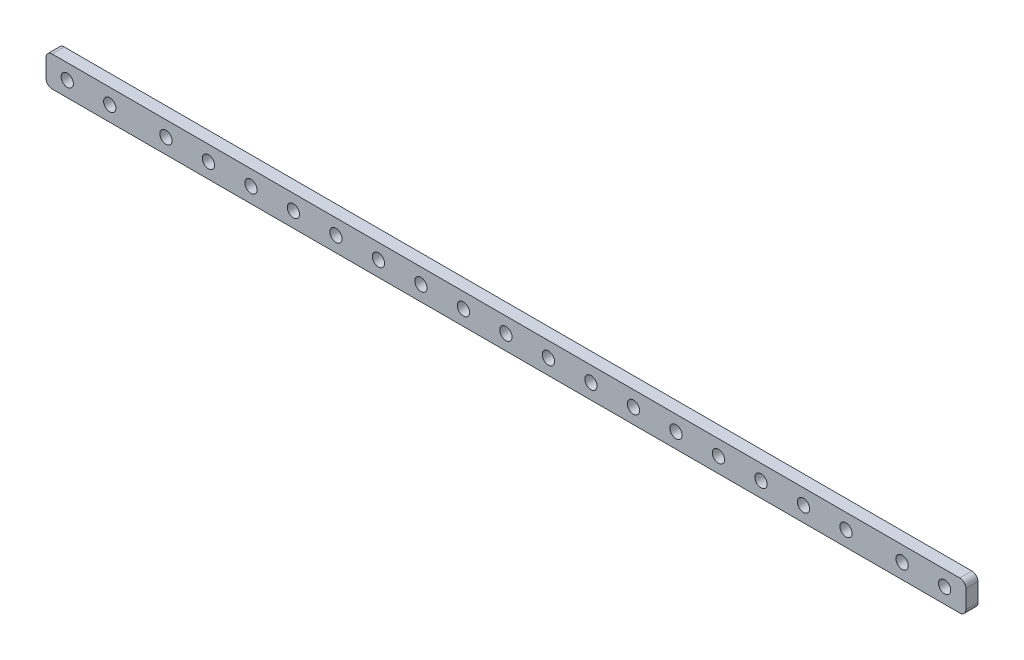
SolidWorks part; units mm, degrees
material "Thornel Mat VMA"
ref_plane "前视基准面" through (0, 0, 0) normal (0, 0, 1) x (1, 0, 0)
ref_plane "上视基准面" through (0, 0, 0) normal (0, 1, 0) x (1, 0, 0)
ref_plane "右视基准面" through (0, 0, 0) normal (1, 0, 0) x (0, 0, -1)
other "Configuration Table"
sketch "草图1" plane through (0, 0, 0) normal (0, 0, 1) x (1, 0, 0)
  line L0 (0, 0) -> (18783.9692, 0) construction
  line L1 (0, 0) -> (0, -50000) construction
  line L2 (-151.5, -5) -> (151.5, -5)
  line L3 (-151.5, -5) -> (-151.5, 5)
  line L4 (-151.5, 5) -> (151.5, 5)
  line L5 (151.5, -5) -> (151.5, 5)
  line L6 (-151.5, -5) -> (151.5, 5) construction
  line L7 (-151.5, 5) -> (151.5, -5) construction
  circle A0 centre (-112, 0) radius 2.025
  circle A1 centre (-98, 0) radius 2.025
  circle A2 centre (-84, 0) radius 2.025
  circle A3 centre (-70, 0) radius 2.025
  circle A4 centre (-56, 0) radius 2.025
  circle A5 centre (-42, 0) radius 2.025
  circle A6 centre (-28, 0) radius 2.025
  circle A7 centre (-14, 0) radius 2.025
  circle A8 centre (0, 0) radius 2.025
  circle A9 centre (14, 0) radius 2.025
  circle A10 centre (28, 0) radius 2.025
  circle A11 centre (42, 0) radius 2.025
  circle A12 centre (56, 0) radius 2.025
  circle A13 centre (70, 0) radius 2.025
  circle A14 centre (84, 0) radius 2.025
  circle A15 centre (98, 0) radius 2.025
  circle A16 centre (112, 0) radius 2.025
  circle A22 centre (-144.5, 0) radius 2.025
  circle A23 centre (-130.5, 0) radius 2.025
  circle A24 centre (168, 0) radius 2.025 [skipped]
  circle A25 centre (154, 0) radius 2.025 [skipped]
  circle A26 centre (140, 0) radius 2.025 [skipped]
  circle A27 centre (126, 0) radius 2.025 [skipped]
  circle A28 centre (130.5, 0) radius 2.025
  circle A29 centre (144.5, 0) radius 2.025
  point P3 (0, 0)
  dimension "D1" = 4.05
  dimension "D2" = 5
  dimension "D4" = 14
  dimension "D5" = 14
  dimension "D6" = 144.5
  dimension "D7" = 7
  dimension "D3" = 21
extrude "凸台-拉伸1" add sketch "草图1" along normal blind 4
fillet "圆角1" radius 2 4 edges at (151.5, -5, 2) (-151.5, -5, 2) (151.5, 5, 2) (-151.5, 5, 2)
